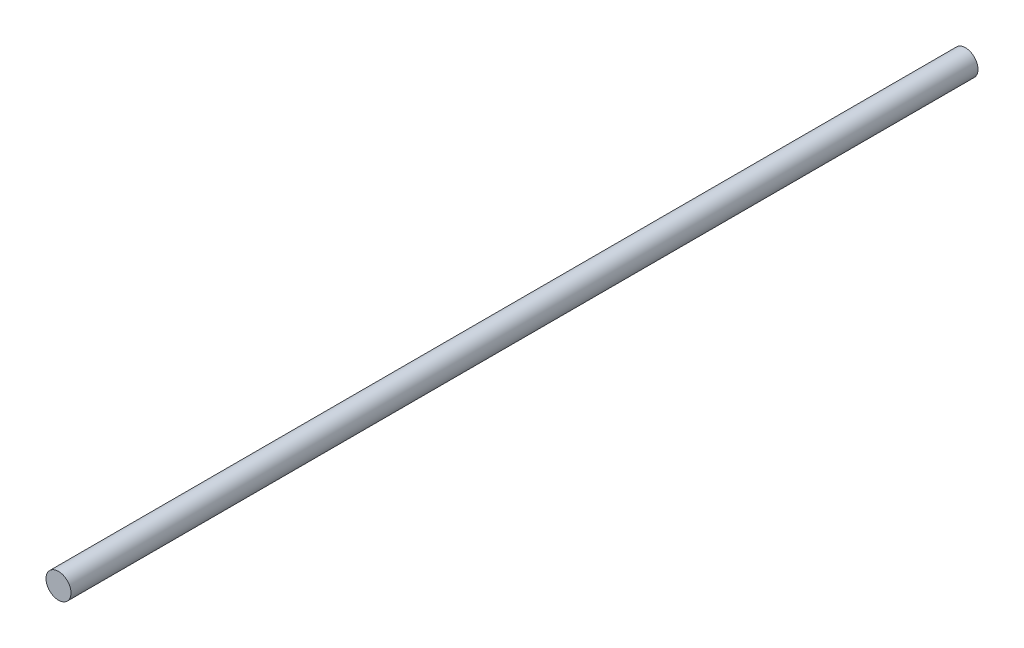
SolidWorks part; units mm, degrees
ref_plane "Plan de face" through (0, 0, 0) normal (0, 0, 1) x (1, 0, 0)
ref_plane "Plan de dessus" through (0, 0, 0) normal (0, 1, 0) x (1, 0, 0)
ref_plane "Plan de droite" through (0, 0, 0) normal (1, 0, 0) x (0, 0, -1)
sketch "Esquisse1" plane through (0, 0, 0) normal (0, 0, 1) x (1, 0, 0)
  circle A0 centre (0, 0) radius 4
  dimension "D1" = 8
extrude "Boss.-Extru.1" add sketch "Esquisse1" along normal blind 290
